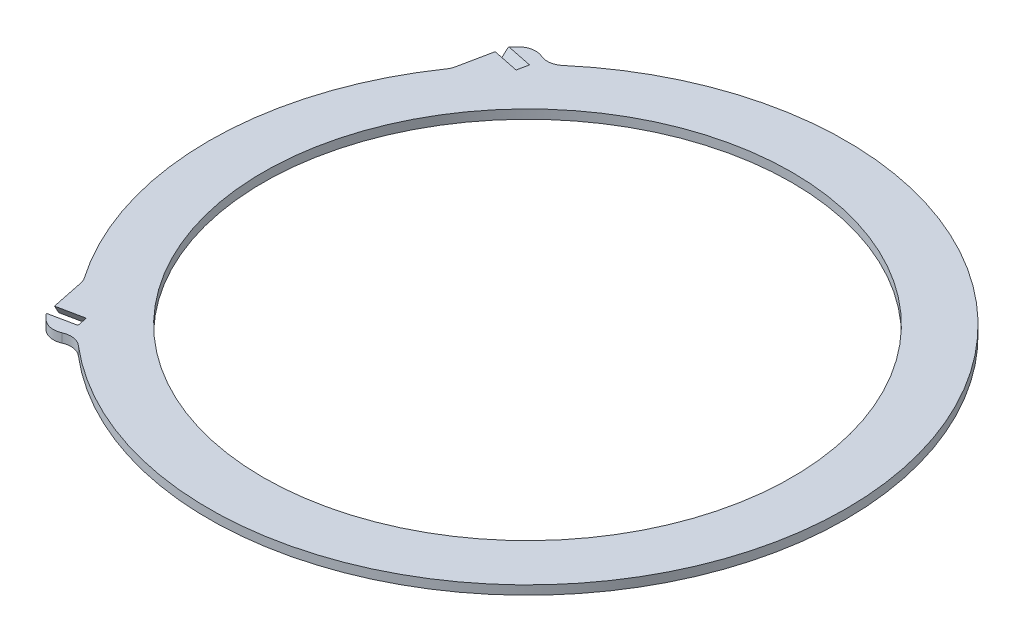
SolidWorks part; units mm, degrees
ref_plane "Front Plane" through (0, 0, 0) normal (0, 0, 1) x (1, 0, 0)
ref_plane "Top Plane" through (0, 0, 0) normal (0, 1, 0) x (1, 0, 0)
ref_plane "Right Plane" through (0, 0, 0) normal (1, 0, 0) x (0, 0, -1)
sketch "Sketch1" plane through (0, 0, 0) normal (0, 1, 0) x (1, 0, 0)
  circle A0 centre (0, 0) radius 295
  circle A1 centre (0, 0) radius 355.5
  dimension "D1" = 590
  dimension "D2" = 711
extrude "Boss-Extrude1" add sketch "Sketch1" along normal blind 10
sketch "Sketch2" plane through (0, 10, 0) normal (0, 1, 0) x (1, 0, 0)
  line L0 (-288.5984, -247.2063) -> (-225.3267, -234.207) construction
  line L1 (-189.1493, -226.7742) -> (-225.3267, -234.207) construction
  line L3 (-185.7973, -238.0877) -> (-279.5847, -257.3566) construction
  line L4 (-182.4679, -237.4036) -> (-214.6628, -244.0182) construction
  line L5 (-259.3109, -277.773) -> (0, 0) construction
  line L6 (-253.5892, -240.0136) -> (-251.2232, -251.5296) construction
  line L7 (-245.2836, -262.747) -> (-201.3072, -215.6396)
  line L9 (-288.5984, -247.2063) -> (-253.5892, -240.0136) construction
  line L10 (-251.2232, -251.5296) -> (-279.5847, -257.3566) construction
  line L11 (-251.2232, -251.5296) -> (-288.5984, -247.2063) construction
  line L12 (-279.5847, -257.3566) -> (-253.5892, -240.0136) construction
  line L13 (-267.9504, -249.5947) -> (0, 0) construction
  line L14 (-288.5984, -247.2063) -> (-279.5847, -257.3566) construction
  line L15 (-279.5847, -257.3566) -> (-281.9507, -245.8405)
  line L16 (-281.9507, -245.8405) -> (-290.3012, -205.1962)
  line L18 (-290.3012, -205.1962) -> (-240.8969, -170.2753)
  arc A0 (-288.5984, -247.2063) -> (-290.4415, -245.0382) centre (0, 0) cw construction
  arc A1 (-279.5847, -257.3566) -> (-274.3423, -262.9378) centre (0, 0) ccw
  arc A2 (-240.8969, -170.2753) -> (-201.3072, -215.6396) centre (0, 0) ccw
  circle A3 centre (0, 0) radius 295 construction
  circle A4 centre (0, 0) radius 355.5 construction
  arc A6 (-274.3423, -262.9378) -> (-245.2836, -262.747) centre (-259.9032, -249.099) ccw
  point P21 (-267.9504, -249.5947)
  dimension "D1" = 4
extrude "Boss-Extrude2" add sketch "Sketch2" against normal blind 10
fillet "Fillet1" radius 20 2 edges at (-242.5922, 5, 259.864) (-290.3012, 5, 205.1962)
ref_plane "Plane1" through (27.6127, -84.8211, 134.3992) normal (0.1712, -0.5258, 0.8332) x (0.9852, 0.0914, -0.1448)
sketch "Sketch5" plane through (27.6127, -84.8211, 134.3992) normal (0.1712, -0.5258, 0.8332) x (0.9852, 0.0914, -0.1448)
  line L0 (-283.2359, 130.8999) -> (-284.8692, 115.7814)
  line L1 (-284.8692, 115.7814) -> (-336.6917, 117.0641)
  line L2 (-283.2359, 130.8999) -> (-281.9732, 142.5885)
  line L3 (-281.9732, 142.5885) -> (-311.7996, 145.8108)
  line L5 (-311.7996, 145.8108) -> (-330.5423, 147.8356)
  line L6 (-330.5423, 147.8356) -> (-336.6917, 117.0641)
extrude "Cut-Extrude2" cut sketch "Sketch5" against normal blind 10
mirror "Mirror1" about plane through (0, 0, 0) normal (0, 0, 1) of "Boss-Extrude2", "Fillet1"
sketch "Sketch7" plane through (21.9514, -85.5807, -106.8442) normal (-0.1583, 0.6173, 0.7706) x (0.9874, 0.099, 0.1236)
  line L0 (317.0049, 82.2589) -> (243.9826, 91.5197)
  line L1 (-213.4127, 149.5272) -> (-307.7845, 161.4956)
  line L2 (-213.4127, 149.5272) -> (-307.7845, 161.4956) construction
  line L3 (317.0049, 82.2589) -> (243.9826, 91.5197)
  line L4 (-307.7845, 161.4956) -> (-278.0229, 157.7212) construction
  line L5 (-278.0229, 157.7212) -> (-276.0135, 173.5657)
  line L6 (-276.0135, 173.5657) -> (-305.7751, 177.3401)
  line L7 (-305.7751, 177.3401) -> (-307.7845, 161.4956)
  line L8 (-310.4097, 140.7956) -> (-280.6481, 137.0212)
  line L9 (-280.6481, 137.0212) -> (-278.0229, 157.7212)
  line L10 (-307.7845, 161.4956) -> (-310.4097, 140.7956)
  dimension "D1" = 30
extrude "Cut-Extrude3" cut sketch "Sketch7" against normal blind 10
